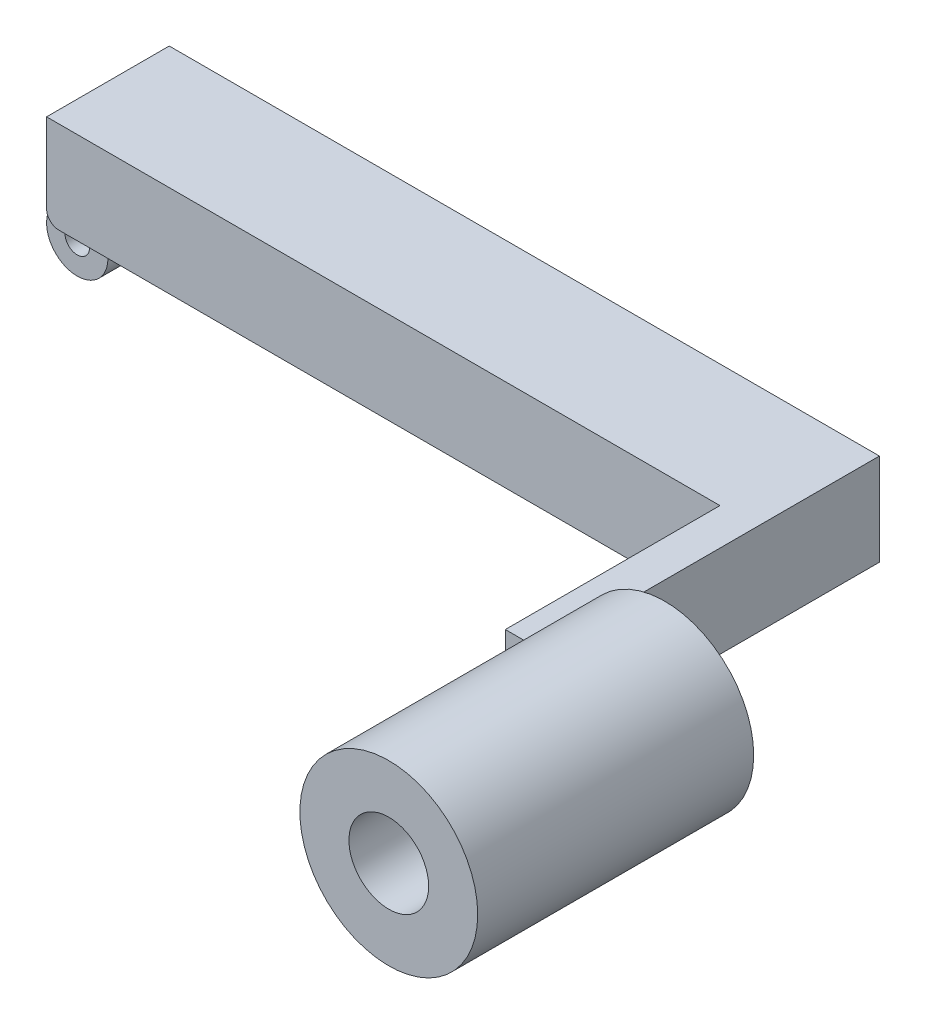
SolidWorks part; units mm, degrees
ref_plane "Front Plane" through (0, 0, 0) normal (0, 0, 1) x (1, 0, 0)
ref_plane "Top Plane" through (0, 0, 0) normal (0, 1, 0) x (1, 0, 0)
ref_plane "Right Plane" through (0, 0, 0) normal (1, 0, 0) x (0, 0, -1)
sketch "Sketch4" plane through (0, 0, 0) normal (1, 0, 0) x (0, 0, -1)
  line L1 (-10, -7.5) -> (10, -7.5)
  line L2 (-10, -7.5) -> (-10, 7.5)
  line L3 (-10, 7.5) -> (10, 7.5)
  line L4 (10, -7.5) -> (10, 7.5)
  line L5 (-10, -7.5) -> (10, 7.5) construction
  line L6 (-10, 7.5) -> (10, -7.5) construction
  point P0 (0, 0)
  dimension "D1" = 20
  dimension "D2" = 15
extrude "Boss-Extrude1" add sketch "Sketch4" along normal blind 115.8
sketch "Sketch5" plane through (0, 0, 10) normal (0, 0, 1) x (1, 0, 0)
  line L0 (115.8, -7.5) -> (0, -7.5) construction
  line L1 (115.8, 7.5) -> (109.8, 7.5)
  line L2 (115.8, 7.5) -> (115.8, -7.5)
  line L3 (115.8, -7.5) -> (109.8, -7.5)
  line L4 (109.8, 7.5) -> (109.8, -7.5)
  dimension "D1" = 6
extrude "Boss-Extrude2" add sketch "Sketch5" along normal blind 35
sketch "Sketch6" plane through (0, 0, 45) normal (0, 0, 1) x (1, 0, 0)
  line L0 (115.8, -7.5) -> (115.8, 7.5) construction
  circle A0 centre (125.8, 0) radius 6.5
  circle A1 centre (125.8, 0) radius 14.5
  point P6 (115.8, 0)
  dimension "D3" = 13
  dimension "D2" = 10
  dimension "D1" = 8
extrude "Boss-Extrude3" add sketch "Sketch6" against normal blind 10 and the other way blind 35
sketch "Sketch7" plane through (0, 0, 0) normal (0, 0, 1) x (1, 0, 0)
  line L0 (5, -12.5) -> (5, -7.5)
  line L1 (109.8, -7.5) -> (0, -7.5) construction
  line L2 (0, 7.5) -> (0, -7.5) construction
  line L3 (0, -7.5) -> (5, -7.5)
  circle A0 centre (0, -12.5) radius 2
  arc A2 (0, -7.5) -> (5, -12.5) centre (0, -12.5) ccw
  circle A3 centre (0, -12.5) radius 5 construction
  arc A4 (0, -7.5) -> (5, -12.5) centre (0, -12.5) cw construction
  dimension "D1" = 4
  dimension "D2" = 3
extrude "Boss-Extrude4" add sketch "Sketch7" along normal mid plane 10
fillet "Fillet1" radius 2 2 edges at (0, -7.5, -7.5) (0, -7.5, 7.5)
